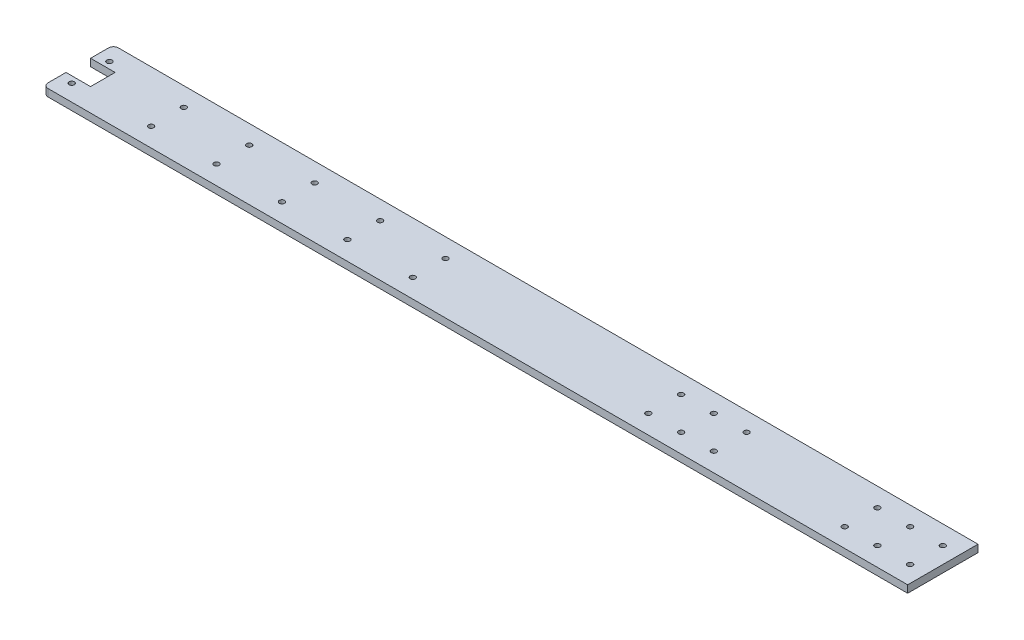
SolidWorks part; units mm, degrees
ref_plane "Front Plane" through (0, 0, 0) normal (0, 0, 1) x (1, 0, 0)
ref_plane "Top Plane" through (0, 0, 0) normal (0, 1, 0) x (1, 0, 0)
ref_plane "Right Plane" through (0, 0, 0) normal (1, 0, 0) x (0, 0, -1)
sketch "Sketch1" plane through (0, 0, 0) normal (0, 1, 0) x (1, 0, 0)
  line L0 (-264.25, 0) -> (-5.75, 0) construction
  line L1 (-264.25, -21.5) -> (264.25, -21.5)
  line L2 (-264.25, -21.5) -> (-264.25, 21.5)
  line L3 (-264.25, 21.5) -> (264.25, 21.5)
  line L4 (264.25, -21.5) -> (264.25, 21.5)
  line L5 (-264.25, -21.5) -> (264.25, 21.5) construction
  line L6 (-264.25, 21.5) -> (264.25, -21.5) construction
  line L7 (-5.75, -35) -> (-5.75, 35) construction
  line L8 (-5.75, 21.5) -> (-5.75, -21.5) construction
  circle A0 centre (-209.75, 10) radius 1.6
  circle A2 centre (-169.75, 10) radius 1.6
  circle A3 centre (-129.75, 10) radius 1.6
  circle A4 centre (-89.75, 10) radius 1.6
  circle A5 centre (-49.75, 10) radius 1.6
  circle A8 centre (-169.75, -10) radius 1.6
  circle A9 centre (-129.75, -10) radius 1.6
  circle A10 centre (-89.75, -10) radius 1.6
  circle A11 centre (-49.75, -10) radius 1.6
  circle A14 centre (-209.75, -10) radius 1.6
  circle A15 centre (234.25, 10) radius 1.6
  circle A16 centre (114.25, 10) radius 1.6
  circle A17 centre (114.25, -10) radius 1.6
  circle A18 centre (234.25, -10) radius 1.6
  circle A19 centre (134.25, -10) radius 1.6
  circle A20 centre (134.25, 10) radius 1.6
  circle A21 centre (254.25, 10) radius 1.6
  circle A22 centre (254.25, -10) radius 1.6
  circle A23 centre (94.25, -10) radius 1.6
  circle A24 centre (94.25, 10) radius 1.6
  circle A25 centre (214.25, 10) radius 1.6
  circle A26 centre (214.25, -10) radius 1.6
  point P0 (0, 0)
  dimension "D4" = 3.2
  dimension "D5" = 5
  dimension "D1" = 528.5
  dimension "D2" = 43
  dimension "D3" = 10
  dimension "D7" = 54.5
  dimension "D8" = 30
  dimension "D9" = 240
  dimension "D6" = 2
  dimension "D10" = 2
  dimension "D11" = 2
  dimension "D12" = 2
  dimension "D13" = 2
extrude "Boss-Extrude1" add sketch "Sketch1" along normal blind 4.5
sketch "Sketch2" plane through (0, 4.5, 0) normal (0, 1, 0) x (1, 0, 0)
  line L0 (-264.25, 0) -> (-249.25, 0) construction
  line L1 (-264.25, 21.5) -> (-264.25, -21.5) construction
  line L2 (-264.25, -7.5) -> (-249.25, -7.5)
  line L3 (-264.25, 7.5) -> (-249.25, 7.5)
  line L4 (-264.25, -7.5) -> (-264.25, 7.5)
  line L5 (-249.25, -7.5) -> (-249.25, 7.5)
  line L6 (-256.75, 0) -> (-256.75, 11.5) construction
  circle A4 centre (-256.75, 11.5) radius 1.6
  circle A5 centre (-256.75, -11.5) radius 1.6
  dimension "D5" = 3.2
  dimension "D1" = 15
  dimension "D4" = 4
  dimension "D2" = 7.5
  dimension "D3" = 7.5
extrude "Cut-Extrude1" cut sketch "Sketch2" against normal through all
fillet "Fillet1" radius 3 2 edges at (-264.25, 2.25, 21.5) (-264.25, 2.25, -21.5)
